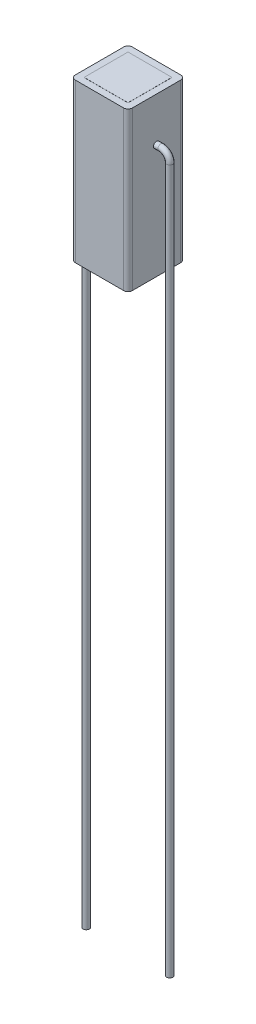
SolidWorks part; units mm, degrees
ref_plane "Front Plane" through (0, 0, 0) normal (0, 0, 1) x (1, 0, 0)
ref_plane "Top Plane" through (0, 0, 0) normal (0, 1, 0) x (1, 0, 0)
ref_plane "Right Plane" through (0, 0, 0) normal (1, 0, 0) x (0, 0, -1)
sketch "Sketch1" plane through (0, 0, 0) normal (0, 1, 0) x (1, 0, 0)
  line L1 (-3.25, 3.25) -> (3.25, 3.25)
  line L2 (-3.25, 3.25) -> (-3.25, -3.25)
  line L3 (-3.25, -3.25) -> (3.25, -3.25)
  line L4 (3.25, 3.25) -> (3.25, -3.25)
  line L5 (-3.25, 3.25) -> (3.25, -3.25) construction
  line L6 (-3.25, -3.25) -> (3.25, 3.25) construction
  point P0 (0, 0)
  dimension "D1" = 6.5
  dimension "D2" = 6.5
sketch "Sketch2" plane through (0, 0, 0) normal (0, 1, 0) x (1, 0, 0)
  line L1 (-2.5, 2.5) -> (2.5, 2.5)
  line L2 (-2.5, 2.5) -> (-2.5, -2.5)
  line L3 (-2.5, -2.5) -> (2.5, -2.5)
  line L4 (2.5, 2.5) -> (2.5, -2.5)
  line L5 (-2.5, 2.5) -> (2.5, -2.5) construction
  line L6 (-2.5, -2.5) -> (2.5, 2.5) construction
  point P0 (0, 0)
extrude "Boss-Extrude1" add sketch "Sketch1" along normal blind 18
extrude "Boss-Extrude2" add sketch "Sketch2" along normal blind 18.01 and the other way blind 0.01
sketch "Sketch3" plane through (3.25, 0, 0) normal (1, 0, 0) x (0, 0, -1)
  line L0 (-3.25, 18) -> (3.25, 18) construction
  line L1 (-3.25, 18) -> (-3.25, 0) construction
  circle A0 centre (0, 13) radius 1
  dimension "D1" = 5
  dimension "D2" = 2
  dimension "D3" = 3.25
sketch "Sketch4" plane through (0, 0, 0) normal (0, 0, 1) x (1, 0, 0)
  line L0 (3.25, 13) -> (3.2, 13)
  line L1 (3.25, 13) -> (3.75, 13)
  line L2 (4.75, 12) -> (4.75, -68.1171)
  arc A0 (3.75, 13) -> (4.75, 12) centre (3.75, 12) cw
  dimension "D1" = 1
sweep "Sweep2" add path "Sketch4" circular profile diameter 0.7 parameters "D3"=0.7
mirror "Mirror1" about plane through (0, 0, 0) normal (1, 0, 0) of "Sweep2", "Boss-Extrude1"
fillet "Fillet2" radius 0.5 4 edges at (3.25, 9, 3.25) (-3.25, 9, 3.25) (-3.25, 9, -3.25) (3.25, 9, -3.25)
